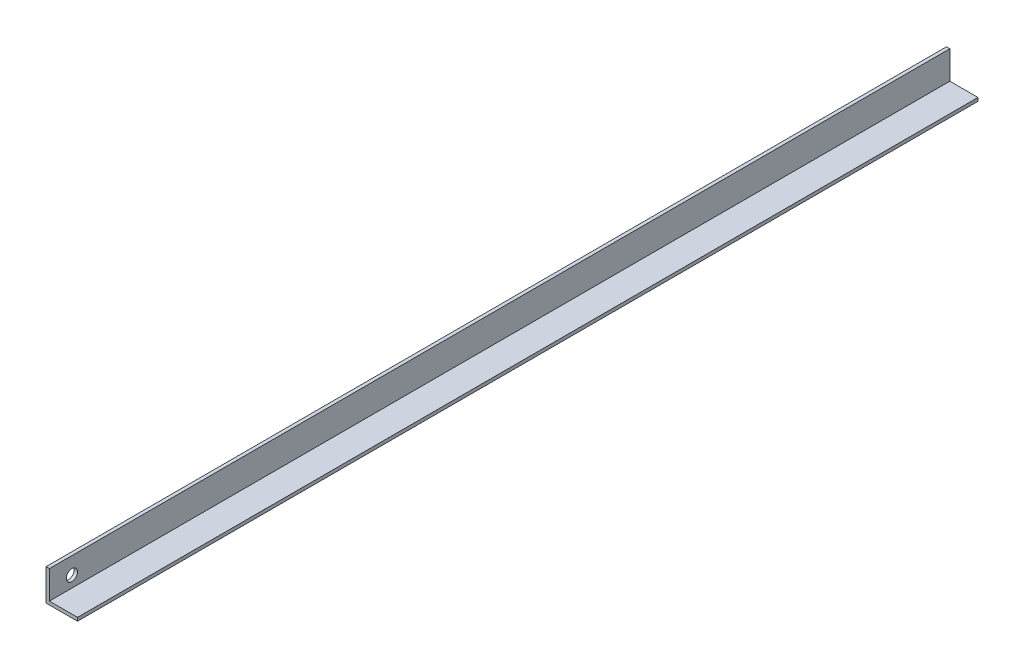
SolidWorks part; units mm, degrees
ref_plane "Спереди" through (0, 0, 0) normal (0, 0, 1) x (1, 0, 0)
ref_plane "Сверху" through (0, 0, 0) normal (0, 1, 0) x (1, 0, 0)
ref_plane "Справа" through (0, 0, 0) normal (1, 0, 0) x (0, 0, -1)
sketch "Эскиз1" plane through (0, 0, 0) normal (0, 0, 1) x (1, 0, 0)
  line L0 (0, 25) -> (0, 0)
  line L1 (0, 0) -> (25, 0)
extrude "Вытянуть-Тонкостенный1" add sketch "Эскиз1" along normal blind 800 thin
sketch "Эскиз2" plane through (-3, 0, 0) normal (1, 0, 0) x (0, 1, 0)
  circle A0 centre (10, 780) radius 5
extrude "Вырез-Вытянуть3" cut sketch "Эскиз2" along normal blind 10
